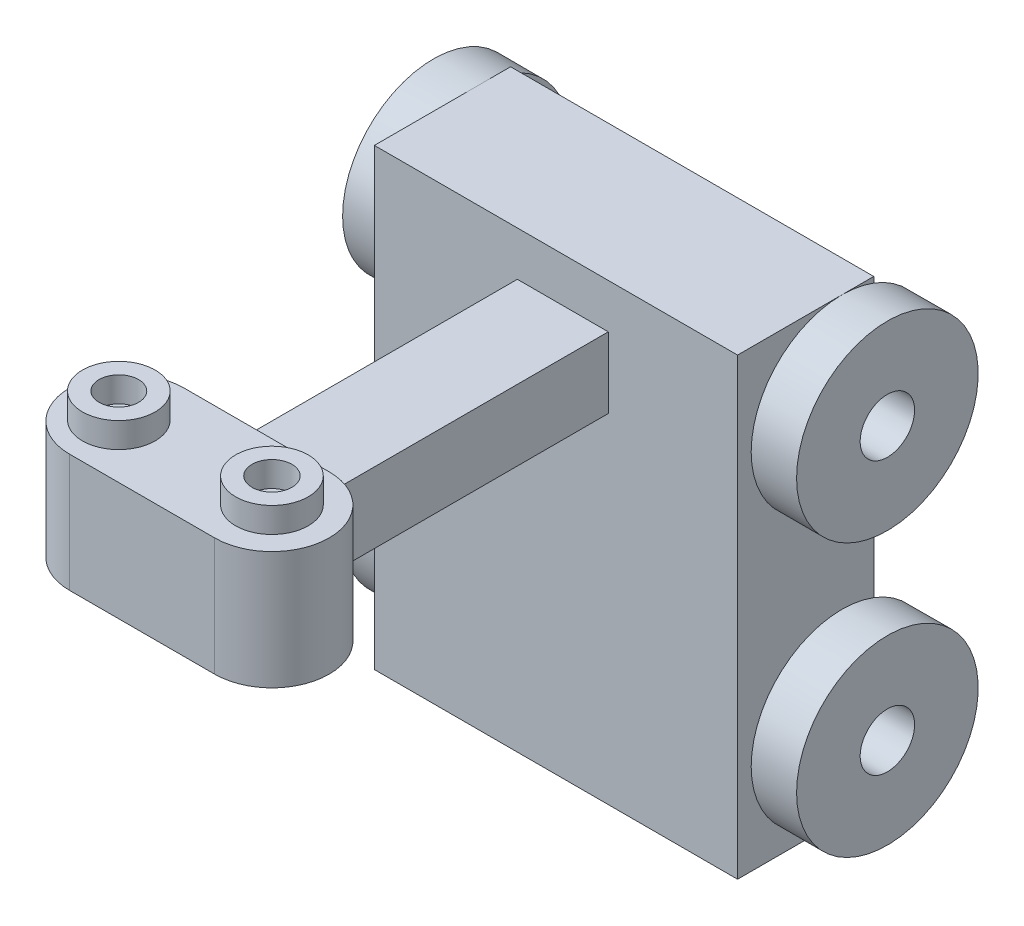
SolidWorks part; units mm, degrees
ref_plane "Front Plane" through (0, 0, 0) normal (0, 0, 1) x (1, 0, 0)
ref_plane "Top Plane" through (0, 0, 0) normal (0, 1, 0) x (1, 0, 0)
ref_plane "Right Plane" through (0, 0, 0) normal (1, 0, 0) x (0, 0, -1)
sketch "Sketch2" plane through (0, 0, 0) normal (0, 0, 1) x (1, 0, 0)
  line L1 (36898.7915, 2293.8889) -> (40898.7915, 2293.8889)
  line L2 (36898.7915, 2293.8889) -> (36898.7915, -2706.1111)
  line L3 (36898.7915, -2706.1111) -> (40898.7915, -2706.1111)
  line L4 (40898.7915, 2293.8889) -> (40898.7915, -2706.1111)
  line L5 (36898.7915, 2293.8889) -> (40898.7915, -2706.1111) construction
  line L6 (36898.7915, -2706.1111) -> (40898.7915, 2293.8889) construction
  circle A0 centre (0, 0) radius 40000
  circle A1 centre (0, 0) radius 38000
  point P4 (38898.7915, -206.1111)
  point P9 (38893.6921, -67.8226)
extrude "Boss-Extrude1" add sketch "Sketch2" along normal blind 1500 contours L2 L1 L4 L3
sketch "Sketch3" plane through (36898.7915, 0, 0) normal (-1, 0, 0) x (0, 0, 1)
  line L0 (750, 2293.8889) -> (750, 1293.8889)
  line L1 (1500, 2293.8889) -> (0, 2293.8889) construction
  line L2 (750, -2706.1111) -> (750, -1706.1111)
  line L3 (1500, -2706.1111) -> (0, -2706.1111) construction
  line L4 (750, 1293.8889) -> (350, 1293.8889)
  line L5 (750, -1706.1111) -> (350, -1706.1111)
  circle A0 centre (350, 1293.8889) radius 1000
  circle A1 centre (350, -1706.1111) radius 1000
  circle A2 centre (350, 1293.8889) radius 300
  circle A3 centre (350, -1706.1111) radius 300
extrude "Boss-Extrude3" add sketch "Sketch3" along normal blind 500 and the other way blind 4500
sketch "Sketch5" plane through (0, 0, 0) normal (0, 0, -1) x (-1, 0, 0)
  line L1 (-40898.7915, 2293.8889) -> (-36898.7915, 2293.8889)
  line L2 (-40898.7915, 2293.8889) -> (-40898.7915, -2706.1111)
  line L3 (-40898.7915, -2706.1111) -> (-36898.7915, -2706.1111)
  line L4 (-36898.7915, 2293.8889) -> (-36898.7915, -2706.1111)
extrude "Cut-Extrude1" cut sketch "Sketch5" along normal blind 2265
sketch "Sketch6" plane through (0, 0, 1500) normal (0, 0, 1) x (1, 0, 0)
  line L1 (38473.4255, 1803.9121) -> (39475.1452, 1803.9121)
  line L2 (38473.4255, 1803.9121) -> (38473.4255, 1024.7968)
  line L3 (38473.4255, 1024.7968) -> (39475.1452, 1024.7968)
  line L4 (39475.1452, 1803.9121) -> (39475.1452, 1024.7968)
extrude "Boss-Extrude4" add sketch "Sketch6" along normal blind 4003
sketch "Sketch7" plane through (0, 1803.9121, 0) normal (0, 1, 0) x (1, 0, 0)
  line L0 (38175.0603, -5503) -> (39773.5104, -5503) construction
  line L3 (39475.1452, -5503) -> (38473.4255, -5503) construction
  line L4 (38175.0603, -4872.5123) -> (39773.5104, -4872.5123)
  line L5 (38175.0603, -6133.4877) -> (39773.5104, -6133.4877)
  arc A2 (38175.0603, -4872.5123) -> (38175.0603, -6133.4877) centre (38175.0603, -5503) ccw
  arc A3 (39773.5104, -6133.4877) -> (39773.5104, -4872.5123) centre (39773.5104, -5503) ccw
  point P6 (38974.2853, -5503)
  point P11 (38974.2853, -5503)
  point P12 (38974.2853, -5503)
extrude "Boss-Extrude5" add sketch "Sketch7" along normal blind 500 and the other way blind 800
sketch "Sketch8" plane through (0, 2303.9121, 0) normal (0, 1, 0) x (1, 0, 0)
  circle A0 centre (38120.6842, -5536.7558) radius 400
  circle A1 centre (39773.5104, -5503) radius 400
  circle A2 centre (38120.6842, -5536.7558) radius 217.789
  circle A3 centre (39773.5104, -5503) radius 220
extrude "Boss-Extrude6" add sketch "Sketch8" along normal blind 277
